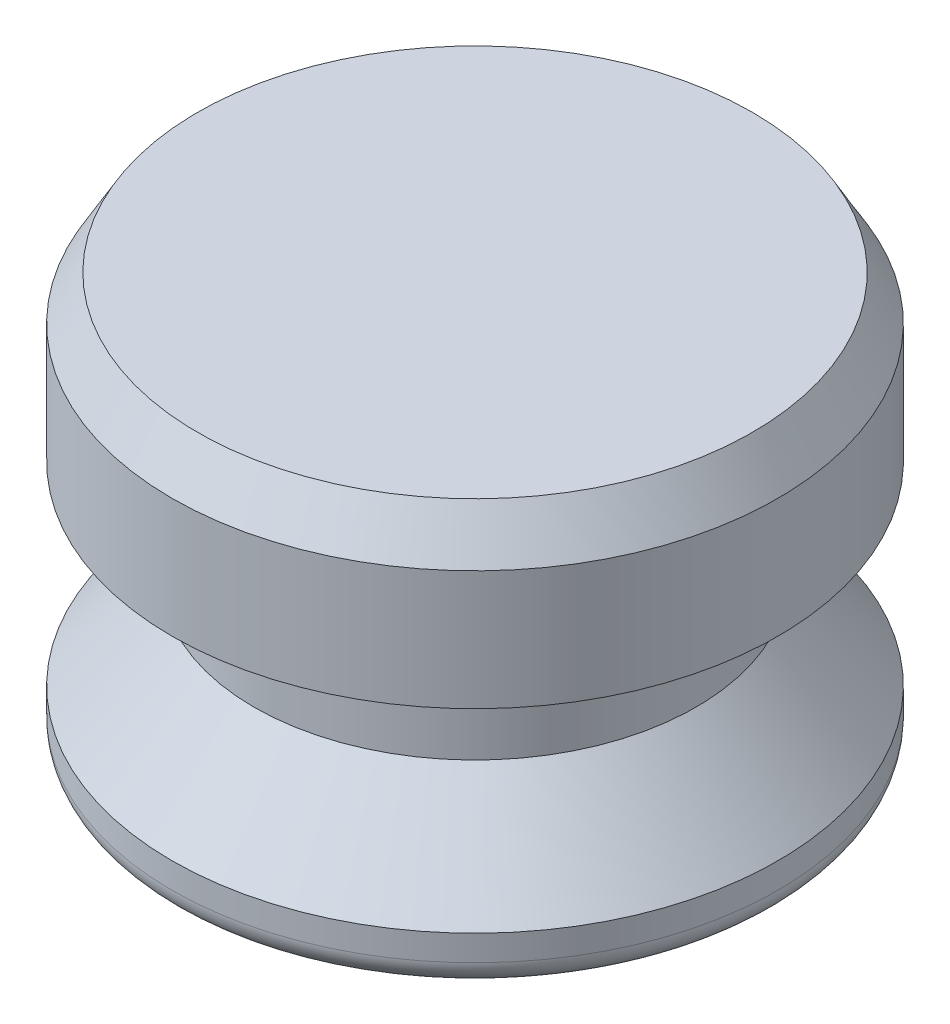
SolidWorks part; units mm, degrees
ref_plane "Front Plane" through (0, 0, 0) normal (0, 0, 1) x (1, 0, 0)
ref_plane "Top Plane" through (0, 0, 0) normal (0, 1, 0) x (1, 0, 0)
ref_plane "Right Plane" through (0, 0, 0) normal (1, 0, 0) x (0, 0, -1)
sketch "Sketch1" plane through (0, 0, 0) normal (0, 0, 1) x (1, 0, 0)
  line L0 (0, 0) -> (0, 12.7) construction
  line L1 (0, 0) -> (-9.398, 0)
  line L2 (-9.398, 0) -> (-9.398, 1.5875)
  line L4 (-6.858, 4.445) -> (-6.858, 7.62)
  line L5 (-6.858, 7.62) -> (-9.398, 7.62)
  line L6 (-9.398, 7.62) -> (-9.398, 12.7)
  line L7 (-9.398, 12.7) -> (0, 12.7)
  line L8 (-9.525, 16.6801) -> (-9.525, -9.6051) construction
  line L9 (0, 0) -> (0, 12.7)
  line L10 (-6.858, 4.445) -> (-9.398, 1.5875)
  dimension "D1" = 12.7
  dimension "D2" = 9.398
  dimension "D3" = 3.175
  dimension "D4" = 1.5875
  dimension "D5" = 9.525
  dimension "D6" = 6.858
  dimension "D7" = 7.62
revolve "Revolve1" add sketch "Sketch1" angle 360 about L9
fillet "Fillet1" radius 0.7937 1 edges at (0, 0, -9.398)
chamfer "Chamfer1" distance 0.7937 angle 60 1 edges at (0, 12.7, -9.398)
